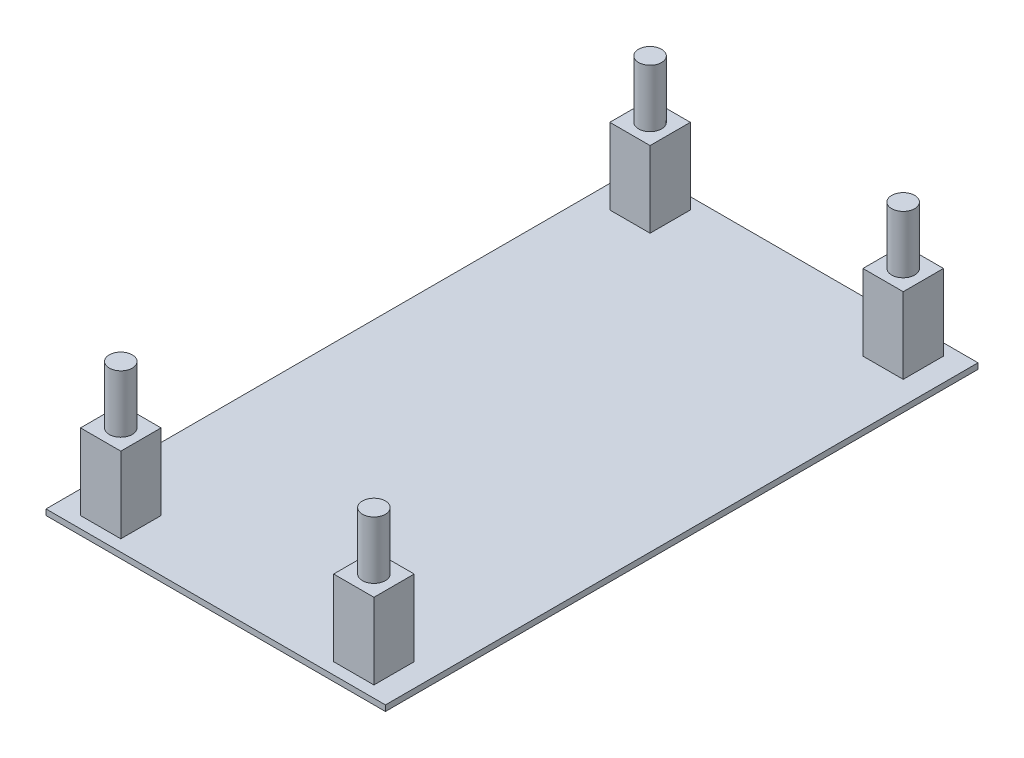
SolidWorks part; units mm, degrees
ref_plane "前视基准面" through (0, 0, 0) normal (0, 0, 1) x (1, 0, 0)
ref_plane "上视基准面" through (0, 0, 0) normal (0, 1, 0) x (1, 0, 0)
ref_plane "右视基准面" through (0, 0, 0) normal (1, 0, 0) x (0, 0, -1)
other "Configuration Table"
sketch "草图1" plane through (0, 0, 0) normal (0, 0, 1) x (1, 0, 0)
  line L1 (-50.7518, 32.0879) -> (89.2482, 32.0879)
  line L2 (-50.7518, 32.0879) -> (-50.7518, -42.9121)
  line L3 (-50.7518, -42.9121) -> (89.2482, -42.9121)
  line L4 (89.2482, 32.0879) -> (89.2482, -42.9121)
  dimension "D1" = 75
  dimension "D2" = 140
extrude "凸台-拉伸1" add sketch "草图1" along normal blind 61
shell "抽壳1" thickness 1.5
sketch "草图3" plane through (0, 0, 0) normal (0, 0, -1) x (-1, 0, 0)
  line L0 (-89.2482, -42.9121) -> (-89.2482, 32.0879) construction
  line L1 (-84.2482, 27.0879) -> (45.7518, 27.0879)
  line L2 (-84.2482, 27.0879) -> (-84.2482, -37.9121)
  line L3 (-84.2482, -37.9121) -> (45.7518, -37.9121)
  line L4 (45.7518, 27.0879) -> (45.7518, -37.9121)
  line L5 (50.7518, -42.9121) -> (-89.2482, -42.9121) construction
  dimension "D1" = 65
  dimension "D2" = 130
  dimension "D3" = 5
  dimension "D4" = 5
extrude "切除-拉伸1" cut sketch "草图3" against normal through all
sketch "草图4" plane through (0, 0, 1.5) normal (0, 0, 1) x (1, 0, 0)
  line L0 (87.7482, -41.4121) -> (87.7482, 30.5879) construction
  line L1 (-49.2518, -41.4121) -> (87.7482, -41.4121)
  line L2 (-49.2518, -41.4121) -> (-49.2518, -38.8121)
  line L3 (-49.2518, -38.8121) -> (87.7482, -38.8121)
  line L4 (87.7482, -41.4121) -> (87.7482, -38.8121)
  line L6 (-49.2518, 27.2879) -> (87.7482, 27.2879)
  line L7 (-49.2518, 27.2879) -> (-49.2518, 30.5879)
  line L8 (-49.2518, 30.5879) -> (87.7482, 30.5879)
  line L9 (87.7482, 27.2879) -> (87.7482, 30.5879)
  dimension "D1" = 2.6
  dimension "D2" = 3.3
extrude "凸台-拉伸2" add sketch "草图4" along normal blind 5
sketch "草图5" plane through (0, 0, 1.5) normal (0, 0, 1) x (1, 0, 0)
  line L0 (87.7482, -38.8121) -> (-49.2518, -38.8121) construction
  line L1 (-49.2518, 30.5879) -> (-46.8518, 30.5879)
  line L2 (-49.2518, 30.5879) -> (-49.2518, -38.8121)
  line L3 (-49.2518, -38.8121) -> (-46.8518, -38.8121)
  line L4 (-46.8518, 30.5879) -> (-46.8518, -38.8121)
  line L6 (87.7482, 30.5879) -> (85.3482, 30.5879)
  line L7 (87.7482, 30.5879) -> (87.7482, -38.8121)
  line L8 (87.7482, -38.8121) -> (85.3482, -38.8121)
  line L9 (85.3482, 30.5879) -> (85.3482, -38.8121)
  dimension "D1" = 2.4
  dimension "D2" = 2.4
extrude "凸台-拉伸3" add sketch "草图5" along normal blind 5
sketch "草图6" plane through (0, -41.4121, 0) normal (0, 1, 0) x (1, 0, 0)
  line L0 (19.2482, -6.5) -> (19.2482, -46.8623) construction
  line L1 (-49.2518, -6.5) -> (87.7482, -6.5) construction
  line L3 (58.2482, -51.5) -> (-19.7518, -51.5)
  line L4 (58.2482, -51.5) -> (58.2482, -9.5)
  line L5 (58.2482, -9.5) -> (-19.7518, -9.5)
  line L6 (-19.7518, -51.5) -> (-19.7518, -9.5)
  line L7 (58.2482, -51.5) -> (-19.7518, -9.5) construction
  line L8 (58.2482, -9.5) -> (-19.7518, -51.5) construction
  point P4 (19.2482, -30.5)
  dimension "D1" = 42
  dimension "D2" = 78
  dimension "D3" = 24
extrude "切除-拉伸2" [suppressed] cut sketch "草图6" against normal through all
sketch "草图20" plane through (0, -41.4121, 0) normal (0, 1, 0) x (1, 0, 0)
  line L0 (-0.5, -11.5) -> (-0.5, -8)
  line L1 (-0.5, -57.5) -> (3, -57.5)
  line L2 (-0.5, -57.5) -> (-0.5, -54)
  line L3 (-0.5, -8) -> (3, -8)
  line L4 (25, -57.5) -> (25, -54)
  line L5 (3, -55.75) -> (21.5, -55.75) construction
  line L6 (-0.5, -57.5) -> (3, -57.5)
  line L7 (-0.5, -57.5) -> (-0.5, -54)
  line L8 (-0.5, -54) -> (3, -54)
  line L9 (3, -57.5) -> (3, -54)
  line L10 (25, -57.5) -> (21.5, -57.5)
  line L11 (25, -57.5) -> (25, -54)
  line L12 (25, -54) -> (21.5, -54)
  line L13 (21.5, -57.5) -> (21.5, -54)
  line L14 (25, -8) -> (21.5, -8)
  line L15 (25, -8) -> (25, -11.5)
  line L16 (25, -11.5) -> (21.5, -11.5)
  line L17 (21.5, -8) -> (21.5, -11.5)
  line L18 (-0.5, -8) -> (3, -8)
  line L19 (-0.5, -8) -> (-0.5, -11.5)
  line L20 (-0.5, -11.5) -> (3, -11.5)
  line L21 (3, -8) -> (3, -11.5)
  line L22 (21.5, -8) -> (25, -8)
  line L23 (25, -11.5) -> (25, -8)
  line L24 (21.5, -57.5) -> (25, -57.5)
  point P18 (12.25, -55.75)
  dimension "D2" = 25.5
  dimension "D3" = 3.5
  dimension "D4" = 3.5
  dimension "D5" = 3.5
  dimension "D6" = 3.5
  dimension "D7" = 3.5
  dimension "D8" = 3.5
  dimension "D9" = 3.5
  dimension "D10" = 3.5
  dimension "D11" = 42.5
extrude "凸台-拉伸4" add sketch "草图20" along normal blind 6.6 contours L1 L9 L8 L2 | L21 L3 L0 L20 | L14 L17 L16 L15 | L11 L10 L13 L12
sketch "草图21" plane through (0, -34.8121, 0) normal (0, 1, 0) x (1, 0, 0)
  circle A2 centre (1.25, -55.75) radius 1
  circle A3 centre (1.25, -9.75) radius 1
  circle A4 centre (23.25, -9.75) radius 1
  circle A5 centre (23.25, -55.75) radius 1
  dimension "D1" = 2
  dimension "D2" = 2
  dimension "D3" = 2
  dimension "D4" = 2
extrude "凸台-拉伸5" add sketch "草图21" along normal blind 5
sketch "草图22" plane through (0, -41.4121, 0) normal (0, 1, 0) x (1, 0, 0)
  line L0 (-0.5, -11.5) -> (-0.5, -8) construction
  line L1 (-2.5, -7) -> (27, -7)
  line L2 (-2.5, -7) -> (-2.5, -58.5)
  line L3 (-2.5, -58.5) -> (27, -58.5)
  line L4 (27, -7) -> (27, -58.5)
  line L5 (25, -8) -> (25, -11.5) construction
  line L6 (-0.5, -8) -> (3, -8) construction
  line L7 (-0.5, -57.5) -> (3, -57.5) construction
  line L9 (-50.7518, 0) -> (89.2482, 0)
  line L10 (-50.7518, 0) -> (-50.7518, -61)
  line L11 (-50.7518, -61) -> (89.2482, -61)
  line L12 (89.2482, 0) -> (89.2482, -61)
  dimension "D1" = 2
  dimension "D2" = 2
  dimension "D3" = 1
  dimension "D4" = 1
extrude "切除-拉伸4" cut sketch "草图22" against normal mid plane 200
sketch "草图23" plane through (0, -42.9121, 0) normal (0, -1, 0) x (1, 0, 0)
  line L1 (-2.5, 58.5) -> (27, 58.5)
  line L2 (-2.5, 58.5) -> (-2.5, 7)
  line L3 (-2.5, 7) -> (27, 7)
  line L4 (27, 58.5) -> (27, 7)
extrude "切除-拉伸5" cut sketch "草图23" against normal blind 1
